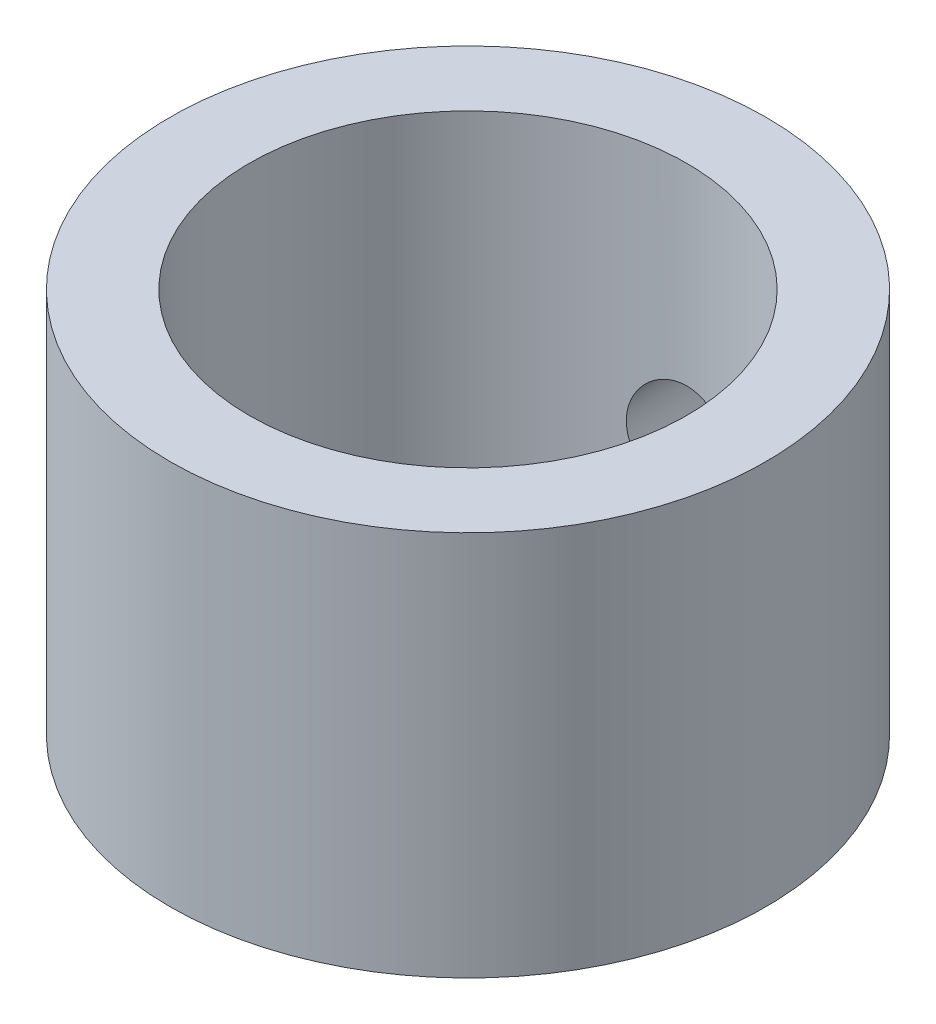
SolidWorks part; units mm, degrees
ref_plane "Front" through (0, 0, 0) normal (0, 0, 1) x (1, 0, 0)
ref_plane "Top" through (0, 0, 0) normal (0, 1, 0) x (1, 0, 0)
ref_plane "Right" through (0, 0, 0) normal (1, 0, 0) x (0, 0, -1)
sketch "Sketch1" plane through (0, 0, 0) normal (0, 1, 0) x (1, 0, 0)
  circle A0 centre (0, 0) radius 6.985
  circle A1 centre (0, 0) radius 9.525
  dimension "D1" = 19.05
  dimension "D2" = 13.97
extrude "Boss-Extrude1" add sketch "Sketch1" along normal blind 4.445
sketch "Sketch3" plane through (0, 4.445, 0) normal (0, 1, 0) x (1, 0, 0)
  circle A0 centre (0, 0) radius 6.985 construction
  circle A1 centre (0, 0) radius 9.525
  circle A2 centre (0, 0) radius 9.525
  circle A3 centre (0, 0) radius 6.985
  dimension "D1" = 0
extrude "Boss-Extrude2" add sketch "Sketch3" along normal blind 6.35
sketch "Sketch2" plane through (0, 0, 0) normal (0, 0, 1) x (1, 0, 0)
  line L2 (-9.525, 0) -> (9.525, 0) construction
  circle A0 centre (0, 4.445) radius 1.7145
  dimension "D1" = 3.429
  dimension "D2" = 4.445
extrude "Cut-Extrude1" cut sketch "Sketch2" against normal through all
sketch "Sketch4" plane through (0, 10.795, 0) normal (0, 1, 0) x (1, 0, 0)
  circle A0 centre (0, 0) radius 6.985 construction
  circle A1 centre (0, 0) radius 9.525
  circle A2 centre (0, 0) radius 9.525
  circle A3 centre (0, 0) radius 6.985
  dimension "D1" = 0
extrude "Boss-Extrude3" add sketch "Sketch4" along normal blind 1.524
